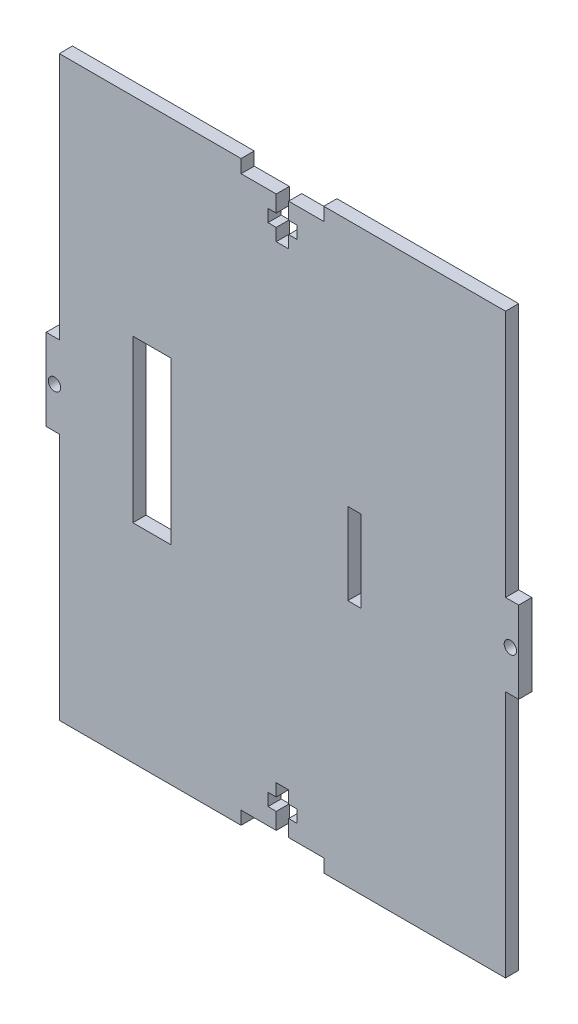
SolidWorks part; units mm, degrees
ref_plane "Front Plane" through (0, 0, 0) normal (0, 0, 1) x (1, 0, 0)
ref_plane "Top Plane" through (0, 0, 0) normal (0, 1, 0) x (1, 0, 0)
ref_plane "Right Plane" through (0, 0, 0) normal (1, 0, 0) x (0, 0, -1)
sketch "Sketch1" plane through (0, 0, 0) normal (0, 0, 1) x (1, 0, 0)
  line L1 (-57.15, 69.85) -> (57.15, 69.85)
  line L2 (-57.15, 69.85) -> (-57.15, -69.85)
  line L3 (-57.15, -69.85) -> (57.15, -69.85)
  line L4 (57.15, 69.85) -> (57.15, -69.85)
  line L5 (-57.15, 69.85) -> (57.15, -69.85) construction
  line L6 (-57.15, -69.85) -> (57.15, 69.85) construction
  point P0 (0, 0)
  dimension "D1" = 139.7
  dimension "D2" = 114.3
extrude "Boss-Extrude1" add sketch "Sketch1" along normal blind 3.18
sketch "Sketch2" plane through (0, 0, 3.18) normal (0, 0, 1) x (1, 0, 0)
  line L0 (0, 0) -> (57.15, 0) construction
  line L1 (-10, 69.85) -> (10, 69.85)
  line L2 (-10, 69.85) -> (-10, 66.67)
  line L3 (-10, 66.67) -> (-1.5, 66.67)
  line L4 (10, 69.85) -> (10, 66.67)
  line L5 (57.15, -69.85) -> (57.15, 69.85) construction
  line L6 (0, 0) -> (0, 69.85) construction
  line L7 (-1.5, 56.67) -> (1.5, 56.67)
  line L8 (-1.5, 56.67) -> (-1.5, 59.67)
  line L10 (1.5, 56.67) -> (1.5, 59.67)
  line L12 (57.15, 69.85) -> (-57.15, 69.85) construction
  line L13 (3.5, 62.67) -> (1.5, 62.67)
  line L14 (3.5, 62.67) -> (3.5, 59.67)
  line L15 (3.5, 59.67) -> (1.5, 59.67)
  line L16 (-3.5, 62.67) -> (-3.5, 59.67)
  line L17 (-10, -69.85) -> (-10, -66.67)
  line L18 (-10, -66.67) -> (-1.5, -66.67)
  line L19 (-1.5, -62.67) -> (-1.5, -66.67)
  line L20 (-1.5, -62.67) -> (-3.5, -62.67)
  line L21 (-3.5, -62.67) -> (-3.5, -59.67)
  line L22 (1.5, 66.67) -> (10, 66.67)
  line L23 (-1.5, 62.67) -> (-3.5, 62.67)
  line L24 (-1.5, -59.67) -> (-3.5, -59.67)
  line L25 (-1.5, -56.67) -> (-1.5, -59.67)
  line L26 (-1.5, -56.67) -> (1.5, -56.67)
  line L27 (-1.5, 59.67) -> (-3.5, 59.67)
  line L28 (1.5, -56.67) -> (1.5, -59.67)
  line L29 (-1.5, 62.67) -> (-1.5, 66.67)
  line L30 (1.5, 62.67) -> (1.5, 66.67)
  line L31 (3.5, -59.67) -> (1.5, -59.67)
  line L32 (3.5, -62.67) -> (3.5, -59.67)
  line L33 (3.5, -62.67) -> (1.5, -62.67)
  line L34 (1.5, -62.67) -> (1.5, -66.67)
  line L35 (1.5, -66.67) -> (10, -66.67)
  line L36 (10, -69.85) -> (10, -66.67)
  line L37 (-10, -69.85) -> (10, -69.85)
  line L38 (-57.15, 69.85) -> (-57.15, -69.85) construction
  line L39 (-57.15, 69.85) -> (-53.97, 69.85)
  line L40 (-57.15, 69.85) -> (-57.15, 9.875)
  line L41 (-57.15, 9.875) -> (-53.97, 9.875)
  line L42 (-53.97, 69.85) -> (-53.97, 9.875)
  line L43 (-57.15, -69.85) -> (-53.97, -69.85)
  line L44 (-57.15, -69.85) -> (-57.15, -9.875)
  line L45 (-57.15, -9.875) -> (-53.97, -9.875)
  line L46 (-53.97, -69.85) -> (-53.97, -9.875)
  line L47 (57.15, -9.875) -> (53.97, -9.875)
  line L48 (53.97, -69.85) -> (53.97, -9.875)
  line L49 (57.15, -69.85) -> (53.97, -69.85)
  line L50 (57.15, -69.85) -> (57.15, -9.875)
  line L51 (57.15, 9.875) -> (53.97, 9.875)
  line L52 (53.97, 69.85) -> (53.97, 9.875)
  line L53 (57.15, 69.85) -> (53.97, 69.85)
  line L54 (57.15, 69.85) -> (57.15, 9.875)
  circle A0 centre (-55.15, 0) radius 1.5
  circle A1 centre (55.15, 0) radius 1.5
  point P0 (0, 50.5662)
  point P5 (0, 32.0079)
  point P10 (15.4931, 34.4893)
  dimension "D11" = 3
  dimension "D12" = 2
  dimension "D1" = 20
  dimension "D2" = 19.75
  dimension "D3" = 4
  dimension "D4" = 3
  dimension "D5" = 3.18
  dimension "D6" = 7
  dimension "D7" = 3
  dimension "D8" = 3
  dimension "D9" = 3.18
  dimension "D10" = 3.18
extrude "Cut-Extrude1" cut sketch "Sketch2" against normal through all
sketch "Sketch3" plane through (0, 0, 0) normal (0, 0, -1) x (-1, 0, 0)
  line L1 (-18.9914, -9.875) -> (-15.8114, -9.875)
  line L2 (-18.9914, -9.875) -> (-18.9914, 9.875)
  line L3 (-18.9914, 9.875) -> (-15.8114, 9.875)
  line L4 (-15.8114, -9.875) -> (-15.8114, 9.875)
extrude "Cut-Extrude2" cut sketch "Sketch3" against normal blind 3.18
sketch "Sketch4" plane through (0, 0, 0) normal (0, 0, -1) x (-1, 0, 0)
  line L1 (26.9743, -19.5467) -> (36.1851, -19.5467)
  line L2 (26.9743, -19.5467) -> (26.9743, 19.5467)
  line L3 (26.9743, 19.5467) -> (36.1851, 19.5467)
  line L4 (36.1851, -19.5467) -> (36.1851, 19.5467)
  line L5 (26.9743, -19.5467) -> (36.1851, 19.5467) construction
  line L6 (26.9743, 19.5467) -> (36.1851, -19.5467) construction
  point P0 (31.5797, 0)
extrude "Cut-Extrude3" cut sketch "Sketch4" against normal blind 3.18
